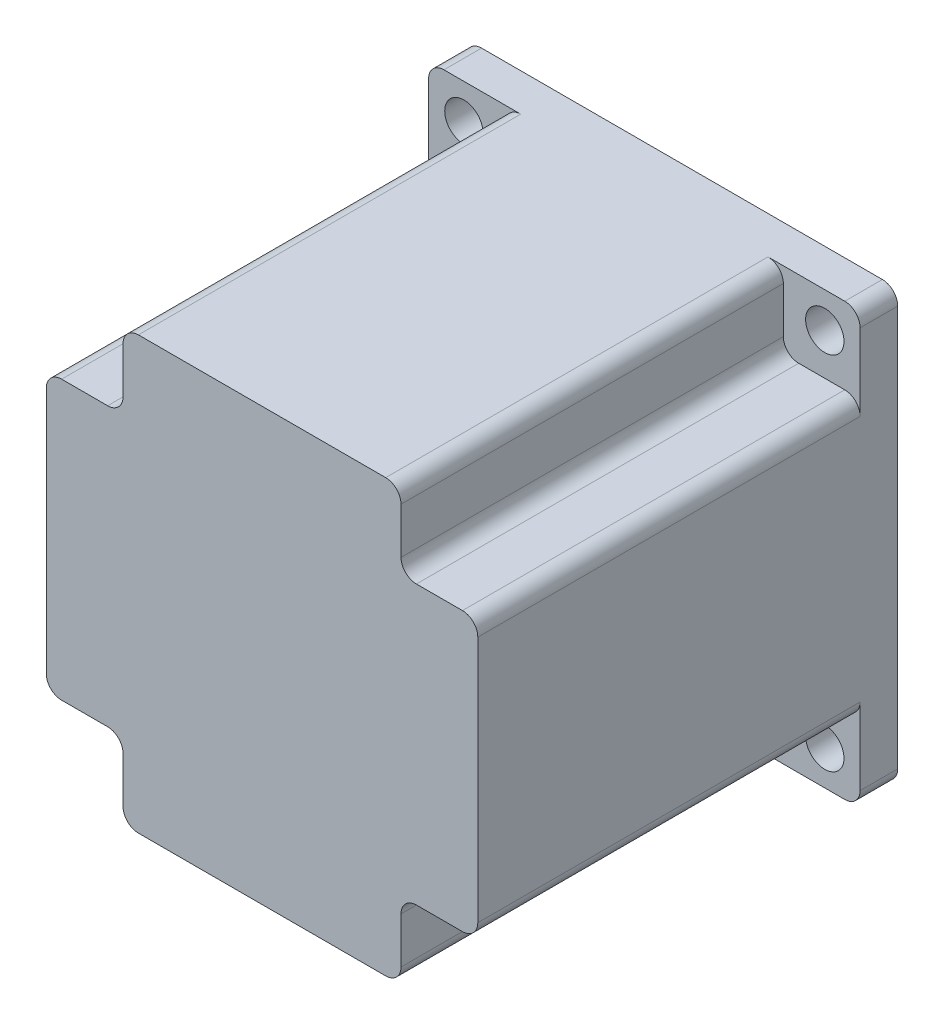
SolidWorks part; units mm, degrees
ref_plane "Front Plane" through (0, 0, 0) normal (0, 0, 1) x (1, 0, 0)
ref_plane "Top Plane" through (0, 0, 0) normal (0, 1, 0) x (1, 0, 0)
ref_plane "Right Plane" through (0, 0, 0) normal (1, 0, 0) x (0, 0, -1)
sketch "Sketch1" plane through (0, 0, 0) normal (0, 0, 1) x (1, 0, 0)
  line L1 (0, 0) -> (56.22, 0)
  line L2 (0, 0) -> (0, 56.22)
  line L3 (0, 56.22) -> (56.22, 56.22)
  line L4 (56.22, 0) -> (56.22, 56.22)
  line L5 (0, 0) -> (56.22, 56.22) construction
  line L6 (0, 56.22) -> (56.22, 0) construction
  point P4 (28.11, 28.11)
  dimension "D1" = 56.22
  dimension "D2" = 56.22
extrude "Boss-Extrude1" add sketch "Sketch1" along normal blind 4.9
sketch "Sketch2" plane through (0, 0, 0) normal (0, 0, -1) x (-1, 0, 0)
  line L0 (-51.62, 28.11) -> (-56.22, 28.11) construction
  line L1 (-51.62, 51.62) -> (-4.6, 51.62) construction
  line L2 (-51.62, 51.62) -> (-51.62, 4.6) construction
  line L3 (-51.62, 4.6) -> (-4.6, 4.6) construction
  line L4 (-4.6, 51.62) -> (-4.6, 4.6) construction
  line L5 (-51.62, 51.62) -> (-4.6, 4.6) construction
  line L6 (-51.62, 4.6) -> (-4.6, 51.62) construction
  line L7 (-56.22, 0) -> (-56.22, 56.22) construction
  line L8 (-21.0175, 51.62) -> (-21.0175, 56.22) construction
  line L9 (-56.22, 56.22) -> (0, 56.22) construction
  line L10 (-4.6, 28.11) -> (0, 28.11) construction
  line L11 (0, 56.22) -> (0, 0) construction
  line L12 (-28.11, 4.6) -> (-28.11, 0) construction
  line L13 (0, 0) -> (-56.22, 0) construction
  circle A0 centre (-4.6, 51.62) radius 2.5
  circle A1 centre (-51.62, 51.62) radius 2.5
  circle A2 centre (-51.62, 4.6) radius 2.5
  circle A3 centre (-4.6, 4.6) radius 2.5
  point P4 (-28.11, 28.11)
  dimension "D1" = 5
  dimension "D2" = 47.02
extrude "Cut-Extrude1" cut sketch "Sketch2" against normal through all
fillet "Fillet1" radius 2 4 edges at (0, 56.22, 2.45) (0, 0, 2.45) (56.22, 0, 2.45) (56.22, 56.22, 2.45)
sketch "Sketch4" plane through (0, 0, 4.9) normal (0, 0, 1) x (1, 0, 0)
  line L0 (0, 28.11) -> (28.11, 28.11)
  line L1 (0, 54.22) -> (0, 2) construction
  line L2 (28.11, 28.11) -> (28.11, 56.22)
  line L3 (54.22, 56.22) -> (2, 56.22) construction
  line L4 (28.11, 56.22) -> (10, 56.22)
  line L5 (10, 56.22) -> (10, 46.22)
  line L6 (10, 46.22) -> (0, 46.22)
  line L7 (0, 46.22) -> (0, 28.11)
  line L8 (46.22, 56.22) -> (28.11, 56.22)
  line L9 (28.11, 56.22) -> (28.11, 28.11)
  line L10 (28.11, 28.11) -> (56.22, 28.11)
  line L11 (56.22, 28.11) -> (56.22, 46.22)
  line L12 (56.22, 46.22) -> (46.22, 46.22)
  line L13 (46.22, 46.22) -> (46.22, 56.22)
  line L14 (56.22, 10) -> (56.22, 28.11)
  line L15 (56.22, 28.11) -> (28.11, 28.11)
  line L16 (28.11, 28.11) -> (28.11, 0)
  line L17 (28.11, 0) -> (46.22, 0)
  line L18 (46.22, 0) -> (46.22, 10)
  line L19 (46.22, 10) -> (56.22, 10)
  line L20 (10, 0) -> (28.11, 0)
  line L21 (28.11, 0) -> (28.11, 28.11)
  line L22 (28.11, 28.11) -> (0, 28.11)
  line L23 (0, 28.11) -> (0, 10)
  line L24 (0, 10) -> (10, 10)
  line L25 (10, 10) -> (10, 0)
  point P28 (28.11, 28.11)
  line M11 (54.22, 56.22) -> (2, 56.22)
  line M13 (0, 54.22) -> (0, 2)
  line M15 (2, 0) -> (54.22, 0)
  line M17 (56.22, 2) -> (56.22, 54.22)
  dimension "D1" = 10
  dimension "D2" = 10
  dimension "D3" = 4
extrude "Boss-Extrude2" add sketch "Sketch4" along normal blind 49.81 contours L5 L6 L0 L2 M13 M11 | L12 L13 L2 L10 M11 M17 | L18 L19 L10 L16 M17 M15 | L24 L25 L16 L0 M15 M13
fillet "Fillet2" radius 2 12 edges at (46.22, 56.22, 29.805) (10, 56.22, 29.805) (0, 46.22, 29.805) (0, 10, 29.805) (10, 0, 29.805) (46.22, 0, 29.805) (56.22, 46.22, 29.805) (56.22, 10, 29.805) (46.22, 46.22, 29.805) (10, 46.22, 29.805) (10, 10, 29.805) (46.22, 10, 29.805)
sketch "Sketch5" plane through (0, 0, 0) normal (0, 0, -1) x (-1, 0, 0)
  circle A0 centre (-28.11, 28.11) radius 19.035
  dimension "D1" = 38.07
extrude "Boss-Extrude3" add sketch "Sketch5" along normal blind 1.6
sketch "Sketch6" plane through (0, 0, -1.6) normal (0, 0, -1) x (-1, 0, 0)
  circle A0 centre (-28.11, 28.11) radius 3.175
  dimension "D1" = 6.35
extrude "Boss-Extrude4" add sketch "Sketch6" along normal blind 19.37
